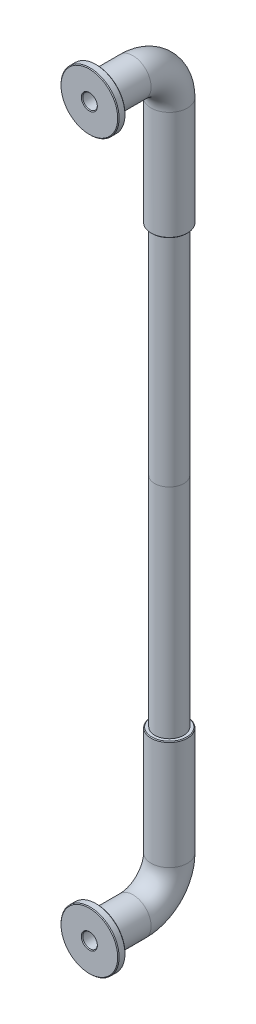
SolidWorks part; units mm, degrees
material "Acciaio inossidabile (ferroso)"
ref_plane "Piano frontale" through (0, 0, 0) normal (0, 0, 1) x (1, 0, 0)
ref_plane "Piano superiore" through (0, 0, 0) normal (0, 1, 0) x (1, 0, 0)
ref_plane "Piano destro" through (0, 0, 0) normal (1, 0, 0) x (0, 0, -1)
sketch "Schizzo1" plane through (0, 0, 0) normal (0, 0, 1) x (1, 0, 0)
  circle A0 centre (0, 0) radius 1
  circle A1 centre (0, 0) radius 2.5
  dimension "D1" = 2
  dimension "D2" = 5
sketch "Schizzo2" plane through (0, 0, 0) normal (1, 0, 0) x (0, 0, -1)
  line L0 (0, 0) -> (5, 0)
  line L1 (0, 2.5) -> (0, -2.5) construction
  line L2 (10, -5) -> (10, -20)
  arc A0 (5, 0) -> (10, -5) centre (5, -5) cw
  point P7 (10, 0)
  dimension "D3" = 5
  dimension "D1" = 10
  dimension "D2" = 20
sweep "Sweep1" add profiles "Schizzo1" path "Schizzo2"
chamfer "Smusso1" distance 0.1 angle 45 1 edges at (2.5, -20, -10)
sketch "Schizzo3" plane through (0, -20, 0) normal (0, -1, 0) x (1, 0, 0)
  circle A0 centre (0, -10) radius 1
  circle A2 centre (0, -10) radius 2
  dimension "D1" = 4
  dimension "D2" = 2
extrude "Estrusione-Estrusione1" add sketch "Schizzo3" along normal blind 30
sketch "Schizzo4" plane through (0, -50, 0) normal (0, -1, 0) x (1, 0, 0)
  circle A0 centre (0, -10) radius 2 construction
  circle A1 centre (0, -10) radius 1 construction
  circle A2 centre (0, -10) radius 2
  circle A3 centre (0, -10) radius 1
extrude "Estrusione-Estrusione2" add sketch "Schizzo4" along normal blind 30 separate body
sketch "Schizzo5" plane through (0, -80, 0) normal (0, -1, 0) x (1, 0, 0)
  circle A0 centre (0, -10) radius 1 construction
  circle A1 centre (0, -10) radius 1
  circle A2 centre (0, -10) radius 2.5
  dimension "D1" = 5
sketch "Schizzo6" plane through (0, 0, 0) normal (1, 0, 0) x (0, 0, -1)
  line L0 (10, -80) -> (10, -95)
  line L2 (7.5, -80) -> (12.5, -80) construction
  line L3 (5, -100) -> (0, -100)
  arc A0 (10, -95) -> (5, -100) centre (5, -95) cw
  point P7 (10, -100)
  dimension "D3" = 5
  dimension "D1" = 10
  dimension "D2" = 20
sweep "Sweep2" add profiles "Schizzo5" path "Schizzo6"
chamfer "Smusso2" distance 0.1 angle 45 1 edges at (0, -80, -12.5)
sketch "Schizzo7" plane through (0, 0, 0) normal (0, 0, 1) x (1, 0, 0)
  circle A0 centre (0, 0) radius 1
  circle A1 centre (0, 0) radius 4
  dimension "D1" = 2
  dimension "D2" = 8
extrude "Estrusione-Estrusione3" add sketch "Schizzo7" along normal blind 1
sketch "Schizzo8" plane through (0, 0, 0) normal (0, 0, 1) x (1, 0, 0)
  circle A0 centre (0, -100) radius 1 construction
  circle A1 centre (0, -100) radius 1
  circle A2 centre (0, -100) radius 4
  dimension "D1" = 8
extrude "Estrusione-Estrusione4" add sketch "Schizzo8" along normal blind 1
chamfer "Smusso3" distance 0.1 angle 45 3 edges at (4, -100, 0) (4, -100, 1) (1, -100, 1)
chamfer "Smusso4" distance 0.1 angle 45 3 edges at (1, 0, 1) (4, 0, 1) (4, 0, 0)
